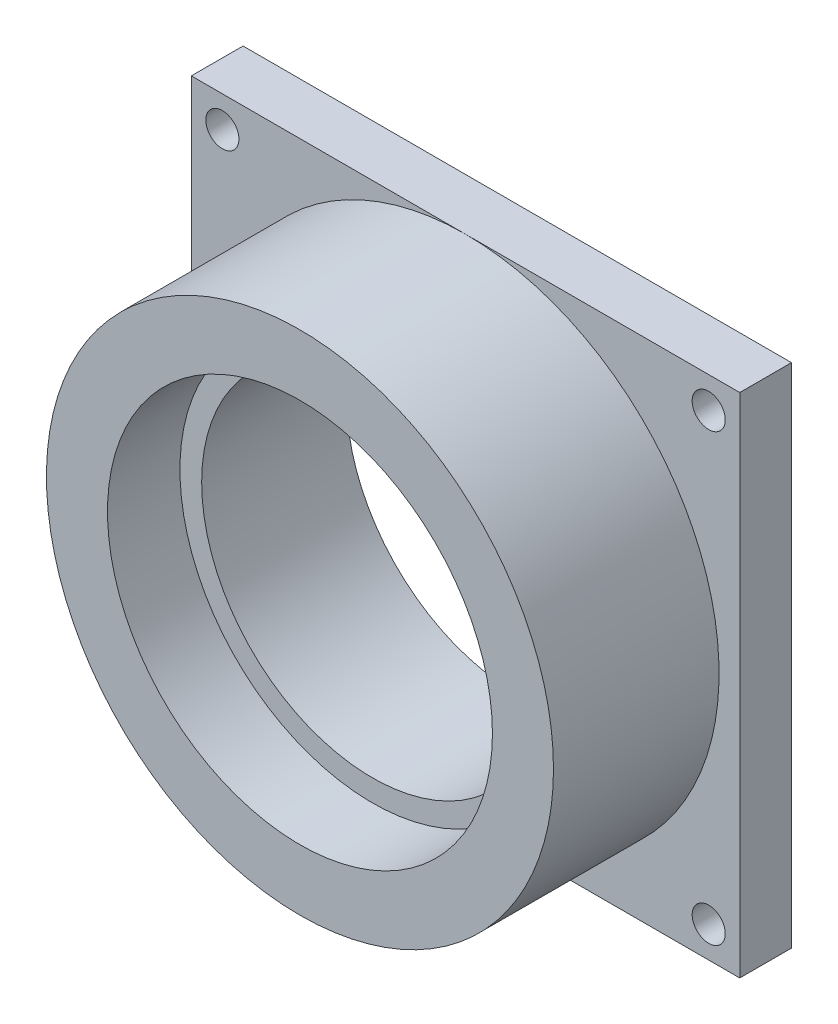
SolidWorks part; units mm, degrees
ref_plane "Front Plane" through (0, 0, 0) normal (0, 0, 1) x (1, 0, 0)
ref_plane "Top Plane" through (0, 0, 0) normal (0, 1, 0) x (1, 0, 0)
ref_plane "Right Plane" through (0, 0, 0) normal (1, 0, 0) x (0, 0, -1)
sketch "Sketch1" plane through (0, 0, 0) normal (0, 0, 1) x (1, 0, 0)
  line L1 (-26.5, -24.5) -> (26.5, -24.5)
  line L2 (-26.5, -24.5) -> (-26.5, 24.5)
  line L3 (-26.5, 24.5) -> (26.5, 24.5)
  line L4 (26.5, -24.5) -> (26.5, 24.5)
  line L5 (0, 24.5) -> (0, -24.5) construction
  line L6 (-26.5, 0) -> (26.5, 0) construction
  point P0 (0, 0)
  dimension "D1" = 49
  dimension "D2" = 53
extrude "Boss-Extrude1" add sketch "Sketch1" along normal blind 5
sketch "Sketch2" plane through (0, 0, 5) normal (0, 0, 1) x (1, 0, 0)
  circle A0 centre (0, 0) radius 24.5
extrude "Boss-Extrude2" add sketch "Sketch2" along normal blind 16
sketch "Sketch4" plane through (0, 0, 0) normal (0, 0, -1) x (-1, 0, 0)
  line L1 (26.5, -24.5) -> (-26.5, -24.5) construction
  line L2 (26.5, 24.5) -> (26.5, -24.5) construction
  circle A0 centre (23.5, -21.5) radius 1.6
  circle A1 centre (-23.5, -21.5) radius 1.6
  circle A2 centre (23.5, 21.5) radius 1.6
  circle A3 centre (-23.5, 21.5) radius 1.6
  dimension "D1" = 3.2
  dimension "D2" = 3
  dimension "D3" = 3
  dimension "D4" = 2
  dimension "D5" = 2
extrude "Cut-Extrude1" cut sketch "Sketch4" against normal through all
sketch "Sketch5" plane through (0, 0, 21) normal (0, 0, 1) x (1, 0, 0)
  circle A0 centre (0, 0) radius 18.6
  dimension "37" = 37.2
extrude "Cut-Extrude2" cut sketch "Sketch5" against normal blind 7
sketch "Sketch6" plane through (0, 0, 14) normal (0, 0, 1) x (1, 0, 0)
  circle A0 centre (0, 0) radius 16.5
  dimension "D1" = 33
extrude "Cut-Extrude3" cut sketch "Sketch6" against normal through all
